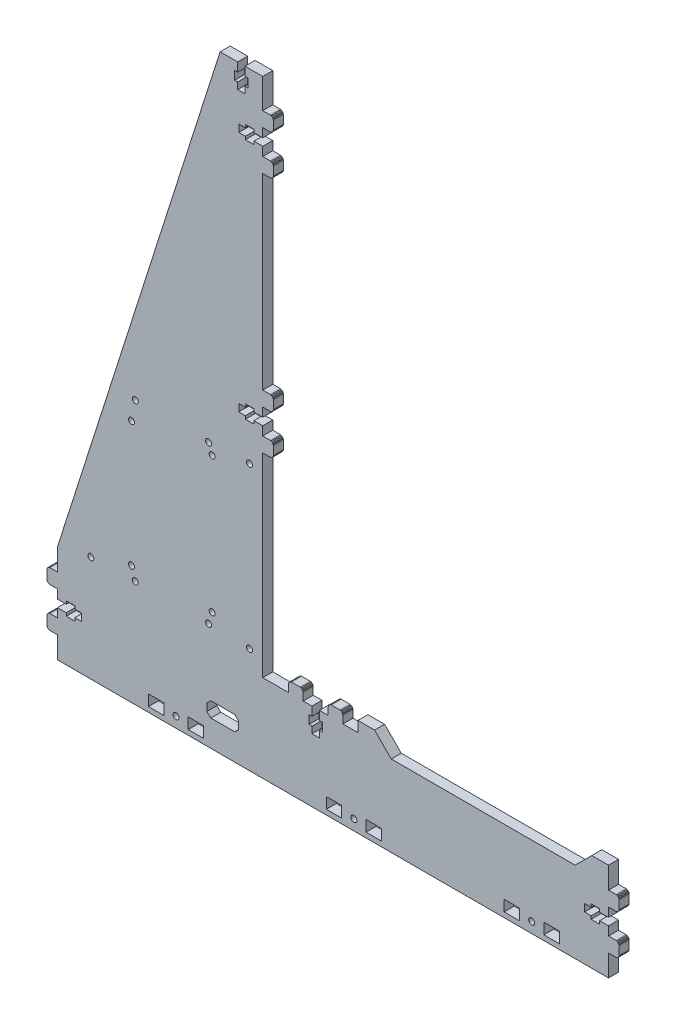
SolidWorks part; units mm, degrees
ref_plane "Plano frontal" through (0, 0, 0) normal (0, 0, 1) x (1, 0, 0)
ref_plane "Plano superior" through (0, 0, 0) normal (0, 1, 0) x (1, 0, 0)
ref_plane "Plano direito" through (0, 0, 0) normal (1, 0, 0) x (0, 0, -1)
sketch "Model" plane through (0, 0, 0) normal (0, 0, 1) x (1, 0, 0)
  line L0 (389.584, 57.2821) -> (389.584, 55.4821)
  line L1 (177.984, 387.9319) -> (167.4757, 387.9319)
  line L2 (70.0841, 36.9821) -> (65.7341, 36.9821)
  line L3 (182.584, 356.0993) -> (178.634, 356.0993)
  line L4 (182.584, 206.832) -> (182.584, 205.032)
  line L5 (399.984, 24.0321) -> (399.984, 36.9821)
  line L6 (182.584, 357.8993) -> (182.584, 356.0993)
  line L7 (192.984, 351.6993) -> (192.984, 346.3993)
  line L8 (187.684, 357.8993) -> (182.584, 357.8993)
  line L9 (177.984, 373.5819) -> (177.984, 377.5319)
  line L10 (84.4341, 55.4821) -> (80.4841, 55.4821)
  line L11 (80.4841, 55.4821) -> (80.4841, 57.2821)
  line L12 (192.984, 370.1993) -> (197.334, 370.1993)
  line L13 (187.684, 213.032) -> (182.584, 213.032)
  line L14 (70.0841, 51.082) -> (75.3841, 51.082)
  line L15 (178.634, 206.832) -> (182.584, 206.832)
  line L16 (187.684, 356.0993) -> (187.684, 357.8993)
  line L17 (399.984, 69.582) -> (399.984, 82.532)
  line L18 (394.684, 49.282) -> (394.684, 51.082)
  line L19 (187.684, 351.6993) -> (192.984, 351.6993)
  line L20 (192.984, 346.3993) -> (197.334, 346.3993)
  line L21 (70.0841, 45.7821) -> (70.0841, 51.082)
  line L22 (84.4341, 51.082) -> (84.4341, 55.4821)
  line L23 (192.984, 211.232) -> (187.684, 211.232)
  line L24 (192.984, 225.332) -> (197.334, 225.332)
  line L25 (178.634, 211.232) -> (178.634, 206.832)
  line L26 (389.584, 49.282) -> (394.684, 49.282)
  line L27 (192.984, 356.0993) -> (187.684, 356.0993)
  line L28 (182.584, 205.032) -> (187.684, 205.032)
  line L29 (182.384, 373.5819) -> (177.984, 373.5819)
  line L30 (182.384, 387.9319) -> (182.384, 382.6319)
  line L31 (80.4841, 57.2821) -> (75.3841, 57.2821)
  line L32 (75.3841, 57.2821) -> (75.3841, 55.4821)
  line L33 (394.684, 51.082) -> (399.984, 51.082)
  line L34 (399.984, 45.7821) -> (399.984, 51.082)
  line L35 (385.634, 51.082) -> (389.584, 51.082)
  line L36 (389.584, 51.082) -> (389.584, 49.282)
  line L37 (178.634, 356.0993) -> (178.634, 351.6993)
  line L38 (187.684, 206.832) -> (192.984, 206.832)
  line L39 (192.984, 201.532) -> (197.334, 201.532)
  line L40 (80.4841, 49.282) -> (80.4841, 51.082)
  line L41 (80.4841, 51.082) -> (84.4341, 51.082)
  line L42 (176.184, 377.5319) -> (176.184, 382.6319)
  line L43 (184.184, 382.6319) -> (184.184, 377.5319)
  line L44 (177.984, 377.5319) -> (176.184, 377.5319)
  line L45 (394.684, 57.2821) -> (389.584, 57.2821)
  line L46 (192.984, 387.9319) -> (182.384, 387.9319)
  line L47 (176.184, 382.6319) -> (177.984, 382.6319)
  line L48 (177.984, 382.6319) -> (177.984, 387.9319)
  line L49 (187.684, 205.032) -> (187.684, 206.832)
  line L50 (182.584, 213.032) -> (182.584, 211.232)
  line L51 (399.984, 45.7821) -> (404.334, 45.7821)
  line L52 (385.634, 55.4821) -> (385.634, 51.082)
  line L53 (192.984, 206.832) -> (192.984, 201.532)
  line L54 (178.634, 351.6993) -> (182.584, 351.6993)
  line L55 (187.684, 349.8993) -> (187.684, 351.6993)
  line L56 (399.984, 55.4821) -> (399.984, 60.782)
  line L57 (70.0841, 55.4821) -> (70.0841, 60.782)
  line L58 (70.0841, 60.782) -> (65.7341, 60.782)
  line L59 (70.0841, 36.9821) -> (70.0841, 24.0321)
  line L60 (75.3841, 51.082) -> (75.3841, 49.282)
  line L61 (75.3841, 49.282) -> (80.4841, 49.282)
  line L62 (70.0841, 69.582) -> (70.0841, 82.532)
  line L63 (192.984, 361.3993) -> (192.984, 356.0993)
  line L64 (167.4757, 387.9319) -> (70.0841, 82.532)
  line L65 (182.584, 211.232) -> (178.634, 211.232)
  line L66 (399.984, 55.4821) -> (394.684, 55.4821)
  line L67 (182.384, 377.5319) -> (182.384, 373.5819)
  line L68 (192.984, 216.532) -> (192.984, 211.232)
  line L69 (389.584, 55.4821) -> (385.634, 55.4821)
  line L70 (184.184, 377.5319) -> (182.384, 377.5319)
  line L71 (182.384, 382.6319) -> (184.184, 382.6319)
  line L72 (394.684, 55.4821) -> (394.684, 57.2821)
  line L73 (399.984, 69.582) -> (404.334, 69.582)
  line L74 (187.684, 211.232) -> (187.684, 213.032)
  line L75 (75.3841, 55.4821) -> (70.0841, 55.4821)
  line L76 (182.584, 351.6993) -> (182.584, 349.8993)
  line L77 (182.584, 349.8993) -> (187.684, 349.8993)
  line L78 (226.884, 70.932) -> (228.684, 70.932)
  line L79 (226.884, 65.832) -> (226.884, 61.882)
  line L80 (240.984, 76.232) -> (240.984, 80.582)
  line L81 (220.684, 65.832) -> (220.684, 70.932)
  line L82 (228.684, 70.932) -> (228.684, 65.832)
  line L83 (220.684, 70.932) -> (222.484, 70.932)
  line L84 (222.484, 61.882) -> (222.484, 65.832)
  line L85 (226.884, 76.232) -> (226.884, 70.932)
  line L86 (222.484, 70.932) -> (222.484, 76.232)
  line L87 (217.184, 76.232) -> (217.184, 80.582)
  line L88 (226.884, 61.882) -> (222.484, 61.882)
  line L89 (222.484, 65.832) -> (220.684, 65.832)
  line L90 (228.684, 65.832) -> (226.884, 65.832)
  line L91 (226.884, 76.232) -> (232.184, 76.232)
  line L92 (217.184, 76.232) -> (222.484, 76.232)
  line L93 (240.984, 76.232) -> (249.9273, 76.232)
  line L94 (197.334, 201.532) -> (197.8517, 201.4639)
  line L95 (197.8517, 201.4639) -> (198.334, 201.2641)
  line L96 (198.334, 201.2641) -> (198.7482, 200.9462)
  line L97 (198.7482, 200.9462) -> (199.0661, 200.532)
  line L98 (199.0661, 200.532) -> (199.2659, 200.0496)
  line L99 (199.334, 199.532) -> (199.334, 194.732)
  line L100 (199.2659, 200.0496) -> (199.334, 199.532)
  line L101 (197.334, 192.732) -> (192.984, 192.732)
  line L102 (197.334, 192.732) -> (197.8517, 192.8002)
  line L103 (197.8517, 192.8002) -> (198.334, 193)
  line L104 (198.334, 193) -> (198.7482, 193.3178)
  line L105 (198.7482, 193.3178) -> (199.0661, 193.732)
  line L106 (199.0661, 193.732) -> (199.2659, 194.2144)
  line L107 (199.2659, 194.2144) -> (199.334, 194.732)
  line L108 (197.334, 346.3993) -> (197.8517, 346.3312)
  line L109 (197.8517, 346.3312) -> (198.334, 346.1314)
  line L110 (198.334, 346.1314) -> (198.7482, 345.8135)
  line L111 (198.7482, 345.8135) -> (199.0661, 345.3993)
  line L112 (199.0661, 345.3993) -> (199.2659, 344.917)
  line L113 (199.334, 344.3993) -> (199.334, 339.5993)
  line L114 (199.2659, 344.917) -> (199.334, 344.3993)
  line L115 (197.334, 361.3993) -> (192.984, 361.3993)
  line L116 (197.334, 361.3993) -> (197.8517, 361.4675)
  line L117 (197.8517, 361.4675) -> (198.334, 361.6673)
  line L118 (198.334, 361.6673) -> (198.7482, 361.9851)
  line L119 (198.7482, 361.9851) -> (199.0661, 362.3993)
  line L120 (199.0661, 362.3993) -> (199.2659, 362.8817)
  line L121 (199.2659, 362.8817) -> (199.334, 363.3993)
  line L122 (406.334, 67.582) -> (406.334, 62.782)
  line L123 (406.334, 67.582) -> (406.2658, 68.0997)
  line L124 (406.2658, 68.0997) -> (406.066, 68.582)
  line L125 (406.066, 68.582) -> (405.7482, 68.9963)
  line L126 (405.7482, 68.9963) -> (405.334, 69.3141)
  line L127 (405.334, 69.3141) -> (404.8516, 69.5139)
  line L128 (404.8516, 69.5139) -> (404.334, 69.582)
  line L129 (404.334, 60.782) -> (399.984, 60.782)
  line L130 (404.334, 60.782) -> (404.8516, 60.8502)
  line L131 (404.8516, 60.8502) -> (405.334, 61.05)
  line L132 (405.334, 61.05) -> (405.7482, 61.3678)
  line L133 (405.7482, 61.3678) -> (406.066, 61.782)
  line L134 (406.066, 61.782) -> (406.2658, 62.2644)
  line L135 (406.2658, 62.2644) -> (406.334, 62.782)
  line L136 (65.7341, 60.782) -> (65.2164, 60.8502)
  line L137 (65.2164, 60.8502) -> (64.7341, 61.05)
  line L138 (64.7341, 61.05) -> (64.3199, 61.3678)
  line L139 (64.3199, 61.3678) -> (64.002, 61.782)
  line L140 (64.002, 61.782) -> (63.8022, 62.2644)
  line L141 (63.7341, 62.782) -> (63.7341, 67.582)
  line L142 (63.8022, 62.2644) -> (63.7341, 62.782)
  line L143 (65.7341, 69.582) -> (70.0841, 69.582)
  line L144 (65.7341, 69.582) -> (65.2164, 69.5139)
  line L145 (65.2164, 69.5139) -> (64.7341, 69.3141)
  line L146 (64.7341, 69.3141) -> (64.3199, 68.9963)
  line L147 (64.3199, 68.9963) -> (64.002, 68.582)
  line L148 (64.002, 68.582) -> (63.8022, 68.0997)
  line L149 (63.8022, 68.0997) -> (63.7341, 67.582)
  line L150 (197.334, 370.1993) -> (197.8517, 370.1312)
  line L151 (197.8517, 370.1312) -> (198.334, 369.9314)
  line L152 (198.334, 369.9314) -> (198.7482, 369.6135)
  line L153 (198.7482, 369.6135) -> (199.0661, 369.1993)
  line L154 (199.0661, 369.1993) -> (199.2659, 368.7169)
  line L155 (199.334, 368.1993) -> (199.334, 363.3993)
  line L156 (199.2659, 368.7169) -> (199.334, 368.1993)
  line L157 (197.334, 337.5993) -> (192.984, 337.5993)
  line L158 (197.334, 337.5993) -> (197.8517, 337.6675)
  line L159 (197.8517, 337.6675) -> (198.334, 337.8673)
  line L160 (198.334, 337.8673) -> (198.7482, 338.1851)
  line L161 (198.7482, 338.1851) -> (199.0661, 338.5993)
  line L162 (199.0661, 338.5993) -> (199.2659, 339.0817)
  line L163 (199.2659, 339.0817) -> (199.334, 339.5993)
  line L164 (63.7341, 43.7821) -> (63.8022, 44.2997)
  line L165 (63.8022, 44.2997) -> (64.002, 44.7821)
  line L166 (64.002, 44.7821) -> (64.3199, 45.1963)
  line L167 (64.3199, 45.1963) -> (64.7341, 45.5141)
  line L168 (64.7341, 45.5141) -> (65.2164, 45.7139)
  line L169 (65.7341, 45.7821) -> (70.0841, 45.7821)
  line L170 (65.2164, 45.7139) -> (65.7341, 45.7821)
  line L171 (240.984, 80.582) -> (240.9159, 81.0997)
  line L172 (240.9159, 81.0997) -> (240.7161, 81.582)
  line L173 (240.7161, 81.582) -> (240.3982, 81.9963)
  line L174 (240.3982, 81.9963) -> (239.984, 82.3141)
  line L175 (239.984, 82.3141) -> (239.5017, 82.5139)
  line L176 (238.984, 82.582) -> (234.184, 82.582)
  line L177 (239.5017, 82.5139) -> (238.984, 82.582)
  line L178 (215.184, 82.582) -> (210.384, 82.582)
  line L179 (215.184, 82.582) -> (215.7017, 82.5139)
  line L180 (215.7017, 82.5139) -> (216.184, 82.3141)
  line L181 (216.184, 82.3141) -> (216.5982, 81.9963)
  line L182 (216.5982, 81.9963) -> (216.9161, 81.582)
  line L183 (216.9161, 81.582) -> (217.1159, 81.0997)
  line L184 (217.1159, 81.0997) -> (217.184, 80.582)
  line L185 (208.384, 80.582) -> (208.384, 76.232)
  line L186 (208.384, 80.582) -> (208.4522, 81.0997)
  line L187 (208.4522, 81.0997) -> (208.652, 81.582)
  line L188 (208.652, 81.582) -> (208.9698, 81.9963)
  line L189 (208.9698, 81.9963) -> (209.384, 82.3141)
  line L190 (209.384, 82.3141) -> (209.8664, 82.5139)
  line L191 (209.8664, 82.5139) -> (210.384, 82.582)
  line L192 (232.184, 80.582) -> (232.184, 76.232)
  line L193 (232.184, 80.582) -> (232.2522, 81.0997)
  line L194 (232.2522, 81.0997) -> (232.452, 81.582)
  line L195 (232.452, 81.582) -> (232.7698, 81.9963)
  line L196 (232.7698, 81.9963) -> (233.184, 82.3141)
  line L197 (233.184, 82.3141) -> (233.6664, 82.5139)
  line L198 (233.6664, 82.5139) -> (234.184, 82.582)
  line L199 (197.334, 216.532) -> (192.984, 216.532)
  line L200 (197.334, 216.532) -> (197.8517, 216.6001)
  line L201 (197.8517, 216.6001) -> (198.334, 216.7999)
  line L202 (198.334, 216.7999) -> (198.7482, 217.1178)
  line L203 (198.7482, 217.1178) -> (199.0661, 217.532)
  line L204 (199.0661, 217.532) -> (199.2659, 218.0144)
  line L205 (199.2659, 218.0144) -> (199.334, 218.532)
  line L206 (249.9273, 82.532) -> (249.9273, 76.232)
  line L207 (65.7341, 36.9821) -> (65.2164, 37.0502)
  line L208 (65.2164, 37.0502) -> (64.7341, 37.25)
  line L209 (64.7341, 37.25) -> (64.3199, 37.5678)
  line L210 (64.3199, 37.5678) -> (64.002, 37.9821)
  line L211 (64.002, 37.9821) -> (63.8022, 38.4644)
  line L212 (63.7341, 38.9821) -> (63.7341, 43.7821)
  line L213 (63.8022, 38.4644) -> (63.7341, 38.9821)
  line L214 (406.334, 38.9821) -> (406.2658, 38.4644)
  line L215 (406.2658, 38.4644) -> (406.066, 37.9821)
  line L216 (406.066, 37.9821) -> (405.7482, 37.5678)
  line L217 (405.7482, 37.5678) -> (405.334, 37.25)
  line L218 (405.334, 37.25) -> (404.8516, 37.0502)
  line L219 (404.334, 36.9821) -> (399.984, 36.9821)
  line L220 (404.8516, 37.0502) -> (404.334, 36.9821)
  line L221 (404.334, 45.7821) -> (404.8516, 45.7139)
  line L222 (404.8516, 45.7139) -> (405.334, 45.5141)
  line L223 (405.334, 45.5141) -> (405.7482, 45.1963)
  line L224 (405.7482, 45.1963) -> (406.066, 44.7821)
  line L225 (406.066, 44.7821) -> (406.2658, 44.2997)
  line L226 (406.334, 43.7821) -> (406.334, 38.9821)
  line L227 (406.2658, 44.2997) -> (406.334, 43.7821)
  line L228 (197.334, 225.332) -> (197.8517, 225.2638)
  line L229 (197.8517, 225.2638) -> (198.334, 225.064)
  line L230 (198.334, 225.064) -> (198.7482, 224.7462)
  line L231 (198.7482, 224.7462) -> (199.0661, 224.332)
  line L232 (199.0661, 224.332) -> (199.2659, 223.8496)
  line L233 (199.334, 223.332) -> (199.334, 218.532)
  line L234 (199.2659, 223.8496) -> (199.334, 223.332)
  line L235 (259.9273, 82.532) -> (269.9273, 72.532)
  line L236 (269.9273, 72.532) -> (379.984, 72.532)
  line L237 (389.984, 82.532) -> (399.984, 82.532)
  line L238 (379.984, 72.532) -> (389.984, 82.532)
  line L239 (337.484, 27.0321) -> (346.684, 27.0321)
  line L240 (346.684, 27.0321) -> (346.684, 33.6321)
  line L241 (254.834, 27.0321) -> (264.034, 27.0321)
  line L242 (124.5841, 33.6321) -> (124.5841, 27.0321)
  line L243 (240.234, 33.6321) -> (231.034, 33.6321)
  line L244 (231.034, 27.0321) -> (240.234, 27.0321)
  line L245 (254.834, 33.6321) -> (254.834, 27.0321)
  line L246 (240.234, 27.0321) -> (240.234, 33.6321)
  line L247 (264.034, 27.0321) -> (264.034, 33.6321)
  line L248 (157.584, 27.0321) -> (157.584, 33.6321)
  line L249 (133.7841, 33.6321) -> (124.5841, 33.6321)
  line L250 (346.684, 33.6321) -> (337.484, 33.6321)
  line L251 (148.3841, 27.0321) -> (157.584, 27.0321)
  line L252 (133.7841, 27.0321) -> (133.7841, 33.6321)
  line L253 (157.584, 33.6321) -> (148.3841, 33.6321)
  line L254 (231.034, 33.6321) -> (231.034, 27.0321)
  line L255 (264.034, 33.6321) -> (254.834, 33.6321)
  line L256 (159.5316, 41.9921) -> (159.5316, 46.4721)
  line L257 (161.9116, 48.7121) -> (176.1868, 48.7121)
  line L258 (176.1868, 39.7521) -> (178.5668, 41.9921)
  line L259 (161.9116, 48.7121) -> (159.5316, 46.4721)
  line L260 (161.9116, 39.7521) -> (176.1868, 39.7521)
  line L261 (178.5668, 46.4721) -> (176.1868, 48.7121)
  line L262 (178.5668, 46.4721) -> (178.5668, 41.9921)
  line L263 (159.5316, 41.9921) -> (161.9116, 39.7521)
  line L264 (361.284, 33.6321) -> (361.284, 27.0321)
  line L265 (370.484, 33.6321) -> (361.284, 33.6321)
  line L266 (337.484, 33.6321) -> (337.484, 27.0321)
  line L267 (361.284, 27.0321) -> (370.484, 27.0321)
  line L268 (148.3841, 33.6321) -> (148.3841, 27.0321)
  line L269 (370.484, 27.0321) -> (370.484, 33.6321)
  line L270 (124.5841, 27.0321) -> (133.7841, 27.0321)
  line L271 (192.984, 387.9319) -> (192.984, 370.1993)
  line L272 (192.984, 76.232) -> (192.984, 192.732)
  line L273 (192.984, 337.5993) -> (192.984, 225.332)
  line L274 (399.984, 24.0321) -> (70.0841, 24.0321)
  line L275 (192.984, 76.232) -> (208.384, 76.232)
  line L276 (259.9273, 82.532) -> (249.9273, 82.532)
  circle A0 centre (353.984, 30.3321) radius 1.8
  circle A1 centre (247.534, 30.3321) radius 1.8
  circle A2 centre (141.0841, 30.3321) radius 1.8
  circle A3 centre (185.0751, 87.2543) radius 1.8
  circle A4 centre (160.5798, 88.0214) radius 1.8
  circle A5 centre (162.7189, 95.0389) radius 1.8
  circle A6 centre (116.6481, 88.0214) radius 1.8
  circle A7 centre (114.4587, 95.1104) radius 1.8
  circle A8 centre (90.0821, 87.2978) radius 1.8
  circle A9 centre (185.0514, 183.2108) radius 1.8
  circle A10 centre (162.689, 176.3556) radius 1.8
  circle A11 centre (160.5477, 182.038) radius 1.8
  circle A12 centre (114.4258, 170.055) radius 1.8
  circle A13 centre (116.7135, 181.9458) radius 1.8
extrude "Ressalto-extrusão1" add sketch "Model" along normal blind 6
